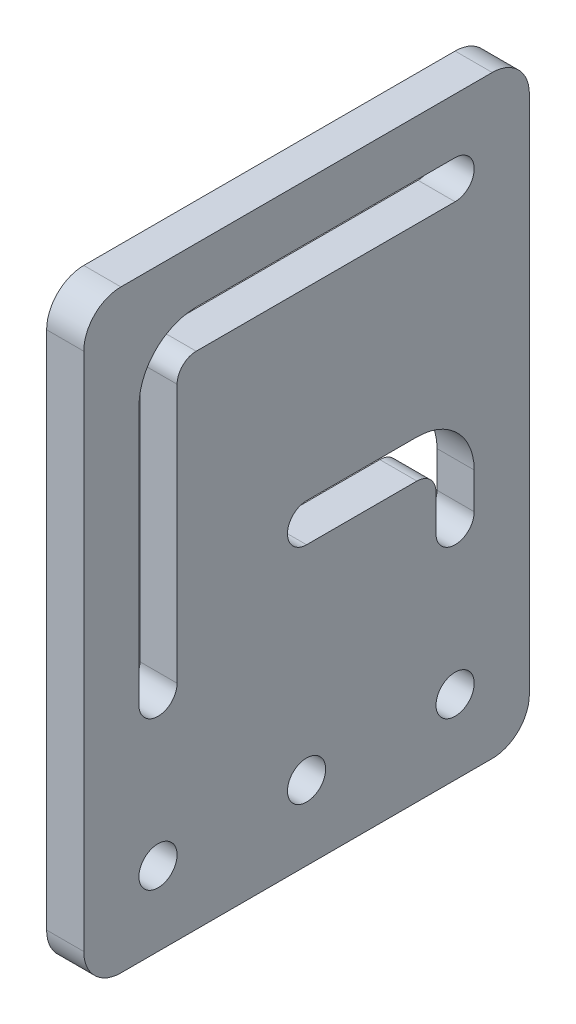
SolidWorks part; units mm, degrees
ref_plane "Front Plane" through (0, 0, 0) normal (0, 0, 1) x (1, 0, 0)
ref_plane "Top Plane" through (0, 0, 0) normal (0, 1, 0) x (1, 0, 0)
ref_plane "Right Plane" through (0, 0, 0) normal (1, 0, 0) x (0, 0, -1)
sketch "Sketch1" plane through (0, 0, 0) normal (1, 0, 0) x (0, 0, -1)
  line L0 (38.1, 101.6) -> (38.1, 0) construction
  line L1 (0, 0) -> (76.2, 0)
  line L2 (0, 0) -> (0, 101.6)
  line L3 (0, 101.6) -> (76.2, 101.6)
  line L4 (76.2, 0) -> (76.2, 101.6)
  line L5 (0, 38.1) -> (76.2, 38.1) construction
  line L6 (38.1, 47.5361) -> (60.2361, 47.5361)
  line L7 (60.2361, 47.5361) -> (60.2361, 38.1)
  line L8 (38.1, 54.0639) -> (66.7639, 54.0639)
  line L9 (66.7639, 54.0639) -> (66.7639, 38.1)
  line L10 (15.9639, 38.1) -> (15.9639, 85.6361)
  line L11 (15.9639, 85.6361) -> (63.5, 85.6361)
  line L12 (9.4361, 38.1) -> (9.4361, 92.1639)
  line L13 (9.4361, 92.1639) -> (63.5, 92.1639)
  circle A0 centre (12.7, 12.7) radius 3.2639
  circle A1 centre (38.1, 12.7) radius 3.2639
  circle A2 centre (63.5, 12.7) radius 3.2639
  arc A3 (9.4361, 38.1) -> (15.9639, 38.1) centre (12.7, 38.1) ccw
  arc A4 (60.2361, 38.1) -> (66.7639, 38.1) centre (63.5, 38.1) ccw
  arc A5 (63.5, 85.6361) -> (63.5, 92.1639) centre (63.5, 88.9) ccw
  arc A7 (38.1, 54.0639) -> (38.1, 47.5361) centre (38.1, 50.8) ccw
  dimension "D3" = 6.5278
  dimension "D8" = 25.4
  dimension "D10" = 6.5278
  dimension "D11" = 6.5278
  dimension "D13" = 6.5278
  dimension "D1" = 76.2
  dimension "D2" = 101.6
  dimension "D4" = 12.7
  dimension "D5" = 12.7
  dimension "D6" = 25.4
  dimension "D7" = 12.7
  dimension "D9" = 12.7
  dimension "D12" = 38.1
  dimension "D14" = 6.5278
extrude "Extrude1" add sketch "Sketch1" along normal blind 6.35
fillet "Fillet2" radius 3.2639 2 edges at (3.175, 47.5361, -60.2361) (3.175, 85.6361, -15.9639)
fillet "Fillet3" radius 9.7917 2 edges at (3.175, 54.0639, -66.7639) (3.175, 92.1639, -9.4361)
fillet "Fillet4" radius 6.35 4 edges at (3.175, 0, 0) (3.175, 0, -76.2) (3.175, 101.6, -76.2) (3.175, 101.6, 0)
